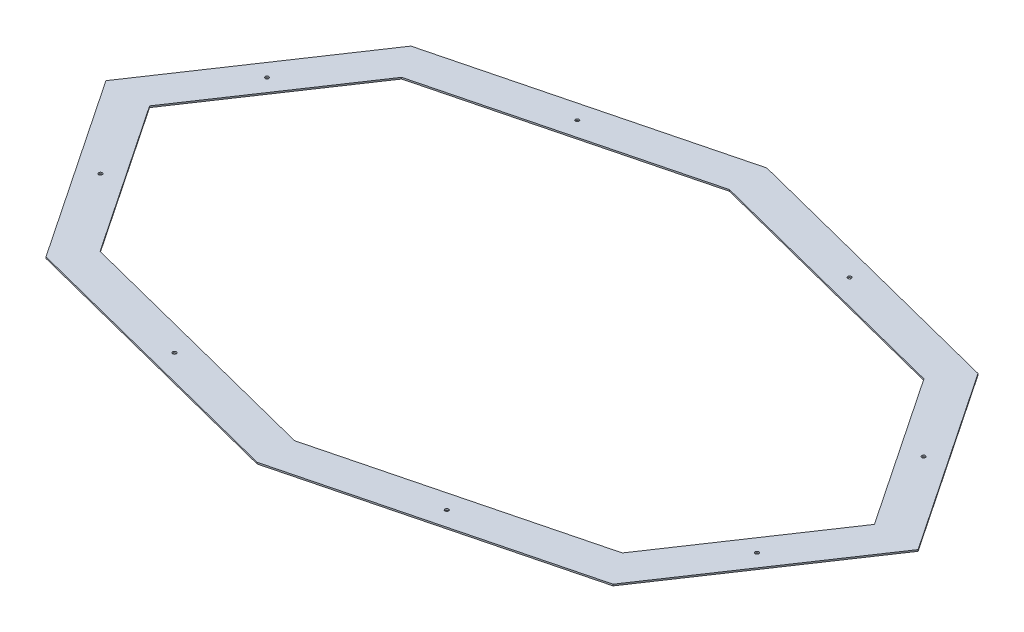
SolidWorks part; units mm, degrees
material "Rubber"
ref_plane "Front Plane" through (0, 0, 0) normal (0, 0, 1) x (1, 0, 0)
ref_plane "Top Plane" through (0, 0, 0) normal (0, 1, 0) x (1, 0, 0)
ref_plane "Right Plane" through (0, 0, 0) normal (1, 0, 0) x (0, 0, -1)
sketch "Sketch2" plane through (0, 0, 0) normal (0, 1, 0) x (1, 0, 0)
  line L0 (0, 0) -> (0, 457.2) construction
  line L1 (-762, 0) -> (-549.0794, 317.0112)
  line L2 (-762, 0) -> (0, 0) construction
  line L3 (549.0794, -317.0112) -> (-549.0794, -317.0112) construction
  line L4 (549.0794, -317.0112) -> (549.0794, 317.0112) construction
  line L5 (549.0794, 317.0112) -> (-549.0794, 317.0112) construction
  line L6 (-549.0794, -317.0112) -> (-549.0794, 317.0112) construction
  line L7 (549.0794, -317.0112) -> (-549.0794, 317.0112) construction
  line L8 (549.0794, 317.0112) -> (-549.0794, -317.0112) construction
  line L9 (-549.0794, 317.0112) -> (0, 457.2)
  line L10 (0, 457.2) -> (549.0794, 317.0112)
  line L11 (549.0794, 317.0112) -> (762, 0)
  line L12 (762, 0) -> (549.0794, -317.0112)
  line L13 (549.0794, -317.0112) -> (0, -457.2)
  line L14 (0, -457.2) -> (-549.0794, -317.0112)
  line L15 (-762, 0) -> (-549.0794, -317.0112)
  line L16 (-596.1161, 383.6463) -> (0, 535.8444)
  line L17 (0, 535.8444) -> (596.1161, 383.6463)
  line L18 (596.1161, 383.6463) -> (853.7922, 0)
  line L19 (853.7922, 0) -> (596.1161, -383.6463)
  line L20 (596.1161, -383.6463) -> (0, -535.8444)
  line L21 (0, -535.8444) -> (-596.1161, -383.6463)
  line L22 (-853.7922, 0) -> (-596.1161, -383.6463)
  line L23 (-853.7922, 0) -> (-596.1161, 383.6463)
  ellipse E0 centre (0, 0) end of major axis (-762, 0) minor radius 457.2 construction
  dimension "D1" = 762
  dimension "D2" = 457.2
  dimension "D3" = 30
  dimension "D4" = 76.2
extrude "Boss-Extrude1" add sketch "Sketch2" along normal mid plane 3.175
sketch "Sketch3" plane through (0, 0, 0) normal (0, 1, 0) x (1, 0, 0)
  line L0 (-572.5978, 350.3287) -> (-807.8961, 0) construction
  line L1 (-807.8961, 0) -> (-572.5978, -350.3287) construction
  line L2 (-572.5978, -350.3287) -> (0, -496.5222) construction
  line L3 (0, -496.5222) -> (572.5978, -350.3287) construction
  line L4 (572.5978, -350.3287) -> (807.8961, 0) construction
  line L5 (807.8961, 0) -> (572.5978, 350.3287) construction
  line L6 (572.5978, 350.3287) -> (0, 496.5222) construction
  line L7 (0, 496.5222) -> (-572.5978, 350.3287) construction
  line L8 (-596.1161, 383.6463) -> (-853.7922, 0)
  line L9 (-853.7922, 0) -> (-596.1161, -383.6463)
  line L10 (-596.1161, -383.6463) -> (0, -535.8444)
  line L11 (0, -535.8444) -> (596.1161, -383.6463)
  line L12 (596.1161, -383.6463) -> (853.7922, 0)
  line L13 (853.7922, 0) -> (596.1161, 383.6463)
  line L14 (596.1161, 383.6463) -> (0, 535.8444)
  line L15 (0, 535.8444) -> (-596.1161, 383.6463)
  line L16 (-596.1161, 383.6463) -> (-853.7922, 0) construction
  line L17 (-853.7922, 0) -> (-596.1161, -383.6463) construction
  line L18 (-596.1161, -383.6463) -> (0, -535.8444) construction
  line L19 (0, -535.8444) -> (596.1161, -383.6463) construction
  line L20 (596.1161, -383.6463) -> (853.7922, 0) construction
  line L21 (853.7922, 0) -> (596.1161, 383.6463) construction
  line L22 (596.1161, 383.6463) -> (0, 535.8444) construction
  line L23 (0, 535.8444) -> (-596.1161, 383.6463) construction
  circle A0 centre (690.2469, 175.1644) radius 3.81
  circle A1 centre (690.2469, -175.1644) radius 3.81
  circle A2 centre (-690.2469, -175.1644) radius 3.81
  circle A3 centre (-690.2469, 175.1644) radius 3.81
  circle A4 centre (-286.2989, 423.4255) radius 3.81
  circle A5 centre (286.2989, 423.4255) radius 3.81
  circle A6 centre (286.2989, -423.4255) radius 3.81
  circle A7 centre (-286.2989, -423.4255) radius 3.81
  dimension "D3" = 7.62
  dimension "D1" = 0
  dimension "D2" = 38.1
extrude "Cut-Extrude1" cut sketch "Sketch3" against normal through all both and the other way through all
